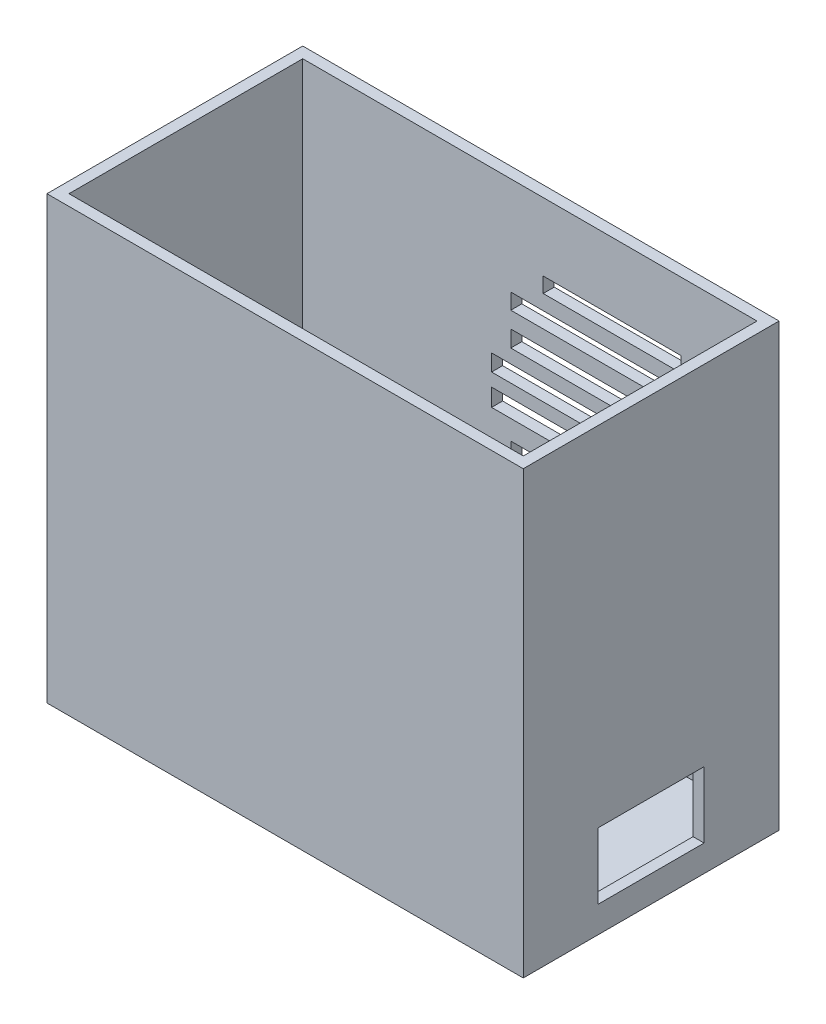
SolidWorks part; units mm, degrees
ref_plane "Front Plane" through (0, 0, 0) normal (0, 0, 1) x (1, 0, 0)
ref_plane "Top Plane" through (0, 0, 0) normal (0, 1, 0) x (1, 0, 0)
ref_plane "Right Plane" through (0, 0, 0) normal (1, 0, 0) x (0, 0, -1)
sketch "Sketch1" plane through (0, 0, 0) normal (0, 1, 0) x (1, 0, 0)
  line L1 (-27, -14.5) -> (27, -14.5)
  line L2 (-27, -14.5) -> (-27, 14.5)
  line L3 (-27, 14.5) -> (27, 14.5)
  line L4 (27, -14.5) -> (27, 14.5)
  line L5 (-27, -14.5) -> (27, 14.5) construction
  line L6 (-27, 14.5) -> (27, -14.5) construction
  point P0 (0, 0)
  dimension "D1" = 54
  dimension "D2" = 29
extrude "Boss-Extrude1" add sketch "Sketch1" along normal blind 50
shell "Shell1" thickness 1.25
sketch "Sketch2" plane through (0, 0, 0) normal (0, -1, 0) x (1, 0, 0)
  line L0 (-27, -14.5) -> (-27, 14.5) construction
  line L1 (11, -10.5) -> (-24.25, -10.5)
  line L2 (11, -10.5) -> (11, 10.5)
  line L3 (11, 10.5) -> (-24.25, 10.5)
  line L4 (-24.25, -10.5) -> (-24.25, 10.5)
  point P6 (11, 0)
  dimension "D1" = 2.75
  dimension "D2" = 35.25
  dimension "sdf" = 21
extrude "Cut-Extrude1" cut sketch "Sketch2" against normal through all
sketch "Sketch3" plane through (27, 0, 0) normal (1, 0, 0) x (0, 0, -1)
  line L0 (-14.5, 0) -> (14.5, 0) construction
  line L1 (6, 10.5) -> (-6, 10.5)
  line L2 (6, 10.5) -> (6, 3)
  line L3 (6, 3) -> (-6, 3)
  line L4 (-6, 10.5) -> (-6, 3)
  point P4 (0, 3)
  point P5 (0, 0)
  dimension "D1" = 12
  dimension "D2" = 7.5
  dimension "D3" = 3
extrude "Cut-Extrude2" cut sketch "Sketch3" against normal up to next
sketch "Sketch4" plane through (0, 0, 0) normal (0, -1, 0) x (1, 0, 0)
  line L0 (11, 10.5) -> (-24.25, 10.5) construction
  line L1 (-13.125, 10.5) -> (-0.125, 10.5)
  line L2 (-13.125, 10.5) -> (-13.125, 12)
  line L3 (-13.125, 12) -> (-0.125, 12)
  line L4 (-0.125, 10.5) -> (-0.125, 12)
  point P6 (-6.625, 10.5)
  point P7 (-6.625, 10.5)
  dimension "D1" = 13
  dimension "D2" = 1.5
extrude "Cut-Extrude3" cut sketch "Sketch4" against normal up to next
sketch "Sketch5" plane through (0, 0, -14.5) normal (0, 0, -1) x (-1, 0, 0)
  circle A0 centre (-8.9153, 30.343) radius 15
  dimension "asdf" = 30
sketch "Sketch6" plane through (0, 0, -14.5) normal (0, 0, -1) x (-1, 0, 0)
  line L1 (-1.5079, 18.4505) -> (-17.1531, 18.4505)
  line L2 (-1.5079, 18.4505) -> (-1.5079, 20.2806)
  line L3 (-1.5079, 20.2806) -> (-17.1531, 20.2806)
  line L4 (-17.1531, 18.4505) -> (-17.1531, 20.2806)
  line L5 (2.1649, 22.1423) -> (-20.4818, 22.1423)
  line L6 (2.1649, 22.1423) -> (2.1649, 24.2588)
  line L7 (2.1649, 24.2588) -> (-20.4818, 24.2588)
  line L8 (-20.4818, 22.1423) -> (-20.4818, 24.2588)
  line L9 (4.3419, 26.4757) -> (-22.3047, 26.4757)
  line L10 (4.3419, 26.4757) -> (4.3419, 28.465)
  line L11 (4.3419, 28.465) -> (-22.3047, 28.465)
  line L12 (-22.3047, 26.4757) -> (-22.3047, 28.465)
  line L13 (4.3419, 29.9461) -> (-22.3047, 29.9461)
  line L14 (4.3419, 29.9461) -> (4.3419, 31.8243)
  line L15 (4.3419, 31.8243) -> (-22.3047, 31.8243)
  line L16 (-22.3047, 29.9461) -> (-22.3047, 31.8243)
  line L17 (2.1649, 33.3903) -> (-20.4818, 33.3903)
  line L18 (2.1649, 33.3903) -> (2.1649, 35.2586)
  line L19 (2.1649, 35.2586) -> (-20.4818, 35.2586)
  line L20 (-20.4818, 33.3903) -> (-20.4818, 35.2586)
  line L21 (2.1649, 37.1034) -> (-20.4818, 37.1034)
  line L22 (2.1649, 37.1034) -> (2.1649, 38.8877)
  line L23 (2.1649, 38.8877) -> (-20.4818, 38.8877)
  line L24 (-20.4818, 37.1034) -> (-20.4818, 38.8877)
  line L25 (-1.5079, 40.5815) -> (-17.1531, 40.5815)
  line L26 (-1.5079, 40.5815) -> (-1.5079, 42.2983)
  line L27 (-1.5079, 42.2983) -> (-17.1531, 42.2983)
  line L28 (-17.1531, 40.5815) -> (-17.1531, 42.2983)
extrude "Cut-Extrude4" cut sketch "Sketch6" against normal up to next
